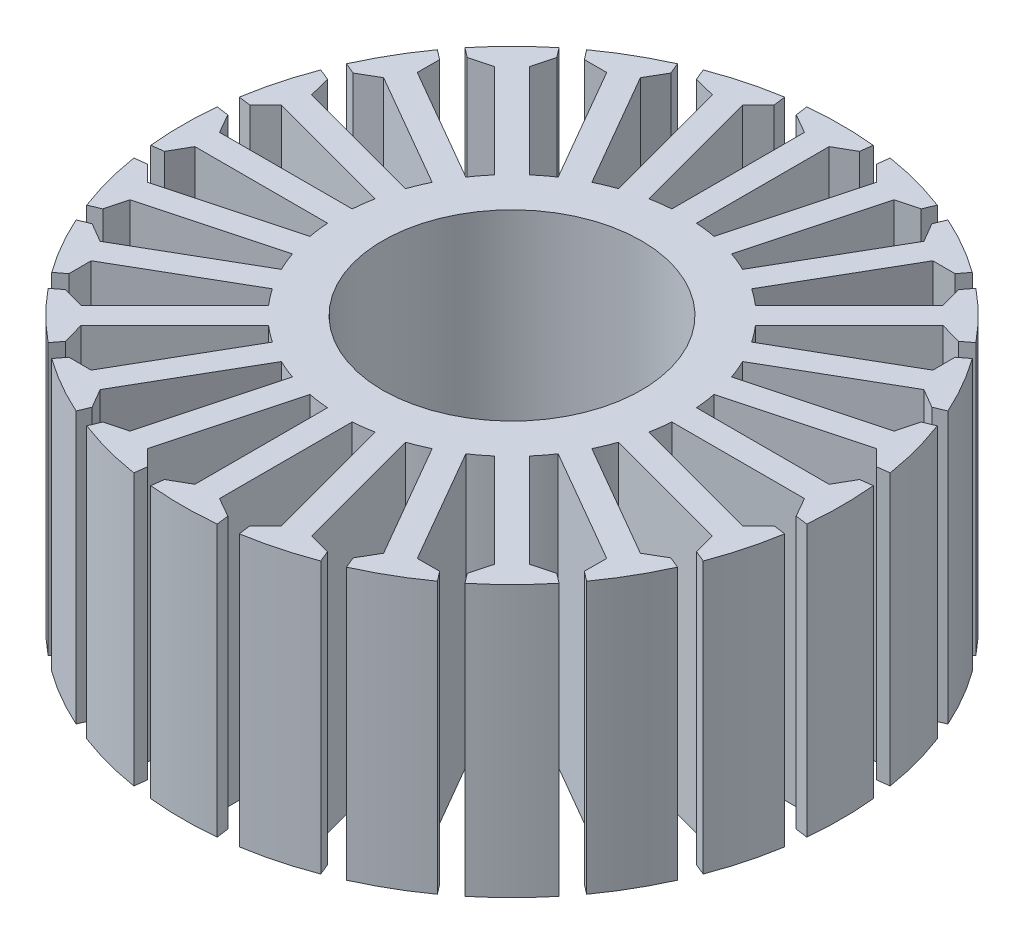
SolidWorks part; units mm, degrees
material "Ductile Iron"
ref_plane "Front Plane" through (0, 0, 0) normal (0, 0, 1) x (1, 0, 0)
ref_plane "Top Plane" through (0, 0, 0) normal (0, 1, 0) x (1, 0, 0)
ref_plane "Right Plane" through (0, 0, 0) normal (1, 0, 0) x (0, 0, -1)
sketch "Sketch3" plane through (0, 0, 0) normal (0, 1, 0) x (1, 0, 0)
  line L0 (0, 0) -> (0, 30) construction
  line L1 (0, 0) -> (8.452, 28.7848) construction
  line L2 (0, 0) -> (16.2192, 25.2376) construction
  line L3 (0, 0) -> (22.6725, 19.6458) construction
  line L4 (0, 0) -> (27.289, 12.4625) construction
  line L5 (0, 0) -> (29.6946, 4.2694) construction
  line L6 (0, 0) -> (29.6946, -4.2694) construction
  line L7 (0, 0) -> (27.289, -12.4625) construction
  line L8 (0, 0) -> (22.6725, -19.6458) construction
  line L9 (0, 0) -> (16.2192, -25.2376) construction
  line L10 (0, 0) -> (8.452, -28.7848) construction
  line L11 (0, 0) -> (0, -30) construction
  line L12 (0, 0) -> (-8.452, -28.7848) construction
  line L13 (0, 0) -> (-16.2192, -25.2376) construction
  line L14 (0, 0) -> (-22.6725, -19.6458) construction
  line L15 (0, 0) -> (-27.289, -12.4625) construction
  line L16 (0, 0) -> (-29.6946, -4.2694) construction
  line L17 (0, 0) -> (-29.6946, 4.2694) construction
  line L18 (0, 0) -> (-27.289, 12.4625) construction
  line L19 (0, 0) -> (-22.6725, 19.6458) construction
  line L20 (0, 0) -> (-16.2192, 25.2376) construction
  line L21 (0, 0) -> (-8.452, 28.7848) construction
  point P26 (0, 0)
  dimension "D1" = 30
  dimension "D2" = 22
sketch "Sketch1" plane through (0, 0, 0) normal (0, 1, 0) x (1, 0, 0)
  line L0 (0, 0) -> (0, 30) construction
  line L1 (3.5544, 26.788) -> (10.3158, 24.9762)
  line L2 (-3.5, 26.7951) -> (3.5, 26.7951)
  line L3 (-3.5, 26.7951) -> (-3.5, 29.7951)
  line L4 (-3.5, 29.7951) -> (3.5, 29.7951)
  line L5 (3.5, 26.7951) -> (3.5, 29.7951)
  line L6 (-3.5, 26.7951) -> (3.5, 29.7951) construction
  line L7 (-3.5, 29.7951) -> (3.5, 26.7951) construction
  line L8 (3.5544, 26.788) -> (4.3308, 29.6858)
  line L9 (4.3308, 29.6858) -> (11.0923, 27.874)
  line L10 (10.3158, 24.9762) -> (11.0923, 27.874)
  line L11 (3.5544, 26.788) -> (11.0923, 27.874) construction
  line L12 (4.3308, 29.6858) -> (10.3158, 24.9762) construction
  line L13 (10.3665, 24.9553) -> (16.4287, 21.4553)
  line L14 (10.3665, 24.9553) -> (11.8665, 27.5533)
  line L15 (11.8665, 27.5533) -> (17.9287, 24.0533)
  line L16 (16.4287, 21.4553) -> (17.9287, 24.0533)
  line L17 (10.3665, 24.9553) -> (17.9287, 24.0533) construction
  line L18 (11.8665, 27.5533) -> (16.4287, 21.4553) construction
  line L19 (16.4721, 21.4219) -> (21.4219, 16.4721)
  line L20 (16.4721, 21.4219) -> (18.5935, 23.5432)
  line L21 (18.5935, 23.5432) -> (23.5432, 18.5935)
  line L22 (21.4219, 16.4721) -> (23.5432, 18.5935)
  line L23 (16.4721, 21.4219) -> (23.5432, 18.5935) construction
  line L24 (18.5935, 23.5432) -> (21.4219, 16.4721) construction
  line L25 (21.4553, 16.4287) -> (24.9553, 10.3665)
  line L26 (21.4553, 16.4287) -> (24.0533, 17.9287)
  line L27 (24.0533, 17.9287) -> (27.5533, 11.8665)
  line L28 (24.9553, 10.3665) -> (27.5533, 11.8665)
  line L29 (21.4553, 16.4287) -> (27.5533, 11.8665) construction
  line L30 (24.0533, 17.9287) -> (24.9553, 10.3665) construction
  line L31 (24.9762, 10.3158) -> (26.788, 3.5544)
  line L32 (24.9762, 10.3158) -> (27.874, 11.0923)
  line L33 (27.874, 11.0923) -> (29.6858, 4.3308)
  line L34 (26.788, 3.5544) -> (29.6858, 4.3308)
  line L35 (24.9762, 10.3158) -> (29.6858, 4.3308) construction
  line L36 (27.874, 11.0923) -> (26.788, 3.5544) construction
  line L37 (26.7951, 3.5) -> (26.7951, -3.5)
  line L38 (26.7951, 3.5) -> (29.7951, 3.5)
  line L39 (29.7951, 3.5) -> (29.7951, -3.5)
  line L40 (26.7951, -3.5) -> (29.7951, -3.5)
  line L41 (26.7951, 3.5) -> (29.7951, -3.5) construction
  line L42 (29.7951, 3.5) -> (26.7951, -3.5) construction
  line L43 (26.788, -3.5544) -> (24.9762, -10.3158)
  line L44 (26.788, -3.5544) -> (29.6858, -4.3308)
  line L45 (29.6858, -4.3308) -> (27.874, -11.0923)
  line L46 (24.9762, -10.3158) -> (27.874, -11.0923)
  line L47 (26.788, -3.5544) -> (27.874, -11.0923) construction
  line L48 (29.6858, -4.3308) -> (24.9762, -10.3158) construction
  line L49 (24.9553, -10.3665) -> (21.4553, -16.4287)
  line L50 (24.9553, -10.3665) -> (27.5533, -11.8665)
  line L51 (27.5533, -11.8665) -> (24.0533, -17.9287)
  line L52 (21.4553, -16.4287) -> (24.0533, -17.9287)
  line L53 (24.9553, -10.3665) -> (24.0533, -17.9287) construction
  line L54 (27.5533, -11.8665) -> (21.4553, -16.4287) construction
  line L55 (21.4219, -16.4721) -> (16.4721, -21.4219)
  line L56 (21.4219, -16.4721) -> (23.5432, -18.5935)
  line L57 (23.5432, -18.5935) -> (18.5935, -23.5432)
  line L58 (16.4721, -21.4219) -> (18.5935, -23.5432)
  line L59 (21.4219, -16.4721) -> (18.5935, -23.5432) construction
  line L60 (23.5432, -18.5935) -> (16.4721, -21.4219) construction
  line L61 (16.4287, -21.4553) -> (10.3665, -24.9553)
  line L62 (16.4287, -21.4553) -> (17.9287, -24.0533)
  line L63 (17.9287, -24.0533) -> (11.8665, -27.5533)
  line L64 (10.3665, -24.9553) -> (11.8665, -27.5533)
  line L65 (16.4287, -21.4553) -> (11.8665, -27.5533) construction
  line L66 (17.9287, -24.0533) -> (10.3665, -24.9553) construction
  line L67 (10.3158, -24.9762) -> (3.5544, -26.788)
  line L68 (10.3158, -24.9762) -> (11.0923, -27.874)
  line L69 (11.0923, -27.874) -> (4.3308, -29.6858)
  line L70 (3.5544, -26.788) -> (4.3308, -29.6858)
  line L71 (10.3158, -24.9762) -> (4.3308, -29.6858) construction
  line L72 (11.0923, -27.874) -> (3.5544, -26.788) construction
  line L73 (3.5, -26.7951) -> (-3.5, -26.7951)
  line L74 (3.5, -26.7951) -> (3.5, -29.7951)
  line L75 (3.5, -29.7951) -> (-3.5, -29.7951)
  line L76 (-3.5, -26.7951) -> (-3.5, -29.7951)
  line L77 (3.5, -26.7951) -> (-3.5, -29.7951) construction
  line L78 (3.5, -29.7951) -> (-3.5, -26.7951) construction
  line L79 (-3.5544, -26.788) -> (-10.3158, -24.9762)
  line L80 (-3.5544, -26.788) -> (-4.3308, -29.6858)
  line L81 (-4.3308, -29.6858) -> (-11.0923, -27.874)
  line L82 (-10.3158, -24.9762) -> (-11.0923, -27.874)
  line L83 (-3.5544, -26.788) -> (-11.0923, -27.874) construction
  line L84 (-4.3308, -29.6858) -> (-10.3158, -24.9762) construction
  line L85 (-10.3665, -24.9553) -> (-16.4287, -21.4553)
  line L86 (-10.3665, -24.9553) -> (-11.8665, -27.5533)
  line L87 (-11.8665, -27.5533) -> (-17.9287, -24.0533)
  line L88 (-16.4287, -21.4553) -> (-17.9287, -24.0533)
  line L89 (-10.3665, -24.9553) -> (-17.9287, -24.0533) construction
  line L90 (-11.8665, -27.5533) -> (-16.4287, -21.4553) construction
  line L91 (-16.4721, -21.4219) -> (-21.4219, -16.4721)
  line L92 (-16.4721, -21.4219) -> (-18.5935, -23.5432)
  line L93 (-18.5935, -23.5432) -> (-23.5432, -18.5935)
  line L94 (-21.4219, -16.4721) -> (-23.5432, -18.5935)
  line L95 (-16.4721, -21.4219) -> (-23.5432, -18.5935) construction
  line L96 (-18.5935, -23.5432) -> (-21.4219, -16.4721) construction
  line L97 (-21.4553, -16.4287) -> (-24.9553, -10.3665)
  line L98 (-21.4553, -16.4287) -> (-24.0533, -17.9287)
  line L99 (-24.0533, -17.9287) -> (-27.5533, -11.8665)
  line L100 (-24.9553, -10.3665) -> (-27.5533, -11.8665)
  line L101 (-21.4553, -16.4287) -> (-27.5533, -11.8665) construction
  line L102 (-24.0533, -17.9287) -> (-24.9553, -10.3665) construction
  line L103 (-24.9762, -10.3158) -> (-26.788, -3.5544)
  line L104 (-24.9762, -10.3158) -> (-27.874, -11.0923)
  line L105 (-27.874, -11.0923) -> (-29.6858, -4.3308)
  line L106 (-26.788, -3.5544) -> (-29.6858, -4.3308)
  line L107 (-24.9762, -10.3158) -> (-29.6858, -4.3308) construction
  line L108 (-27.874, -11.0923) -> (-26.788, -3.5544) construction
  line L109 (-26.7951, -3.5) -> (-26.7951, 3.5)
  line L110 (-26.7951, -3.5) -> (-29.7951, -3.5)
  line L111 (-29.7951, -3.5) -> (-29.7951, 3.5)
  line L112 (-26.7951, 3.5) -> (-29.7951, 3.5)
  line L113 (-26.7951, -3.5) -> (-29.7951, 3.5) construction
  line L114 (-29.7951, -3.5) -> (-26.7951, 3.5) construction
  line L115 (-26.788, 3.5544) -> (-24.9762, 10.3158)
  line L116 (-26.788, 3.5544) -> (-29.6858, 4.3308)
  line L117 (-29.6858, 4.3308) -> (-27.874, 11.0923)
  line L118 (-24.9762, 10.3158) -> (-27.874, 11.0923)
  line L119 (-26.788, 3.5544) -> (-27.874, 11.0923) construction
  line L120 (-29.6858, 4.3308) -> (-24.9762, 10.3158) construction
  line L121 (-24.9553, 10.3665) -> (-21.4553, 16.4287)
  line L122 (-24.9553, 10.3665) -> (-27.5533, 11.8665)
  line L123 (-27.5533, 11.8665) -> (-24.0533, 17.9287)
  line L124 (-21.4553, 16.4287) -> (-24.0533, 17.9287)
  line L125 (-24.9553, 10.3665) -> (-24.0533, 17.9287) construction
  line L126 (-27.5533, 11.8665) -> (-21.4553, 16.4287) construction
  line L127 (-21.4219, 16.4721) -> (-16.4721, 21.4219)
  line L128 (-21.4219, 16.4721) -> (-23.5432, 18.5935)
  line L129 (-23.5432, 18.5935) -> (-18.5935, 23.5432)
  line L130 (-16.4721, 21.4219) -> (-18.5935, 23.5432)
  line L131 (-21.4219, 16.4721) -> (-18.5935, 23.5432) construction
  line L132 (-23.5432, 18.5935) -> (-16.4721, 21.4219) construction
  line L133 (-16.4287, 21.4553) -> (-10.3665, 24.9553)
  line L134 (-16.4287, 21.4553) -> (-17.9287, 24.0533)
  line L135 (-17.9287, 24.0533) -> (-11.8665, 27.5533)
  line L136 (-10.3665, 24.9553) -> (-11.8665, 27.5533)
  line L137 (-16.4287, 21.4553) -> (-11.8665, 27.5533) construction
  line L138 (-17.9287, 24.0533) -> (-10.3665, 24.9553) construction
  line L139 (-10.3158, 24.9762) -> (-3.5544, 26.788)
  line L140 (-10.3158, 24.9762) -> (-11.0923, 27.874)
  line L141 (-11.0923, 27.874) -> (-4.3308, 29.6858)
  line L142 (-3.5544, 26.788) -> (-4.3308, 29.6858)
  line L143 (-10.3158, 24.9762) -> (-4.3308, 29.6858) construction
  line L144 (-11.0923, 27.874) -> (-3.5544, 26.788) construction
  circle A0 centre (0, 0) radius 32.5
  circle A1 centre (0, 0) radius 30
  circle A2 centre (0, 0) radius 10
  circle A3 centre (0, 0) radius 26.6
  point P5 (0, 28.2951)
  point P10 (7.3233, 27.331)
  point P17 (14.1476, 24.5043)
  point P22 (20.0077, 20.0077)
  point P27 (24.5043, 14.1476)
  point P32 (27.331, 7.3233)
  point P37 (28.2951, 0)
  point P42 (27.331, -7.3233)
  point P47 (24.5043, -14.1476)
  point P52 (20.0077, -20.0077)
  point P57 (14.1476, -24.5043)
  point P62 (7.3233, -27.331)
  point P67 (0, -28.2951)
  point P72 (-7.3233, -27.331)
  point P77 (-14.1476, -24.5043)
  point P82 (-20.0077, -20.0077)
  point P87 (-24.5043, -14.1476)
  point P92 (-27.331, -7.3233)
  point P97 (-28.2951, 0)
  point P102 (-27.331, 7.3233)
  point P107 (-24.5043, 14.1476)
  point P112 (-20.0077, 20.0077)
  point P117 (-14.1476, 24.5043)
  point P122 (-7.3233, 27.331)
  point P127 (0, 0)
  dimension "D1" = 65
  dimension "D2" = 60
  dimension "D5" = 20
  dimension "D8" = 53.2
  dimension "D3" = 3
  dimension "D4" = 7
sketch "Sketch4" plane through (0, 0, 0) normal (0, 1, 0) x (1, 0, 0)
  line L0 (0, 0) -> (0, 30) construction
  line L1 (0, 0) -> (0, 24.6)
  line L2 (0, 0) -> (-8.452, 28.7848) construction
  line L3 (0, 0) -> (-6.9306, 23.6035)
  line L5 (-3.7856, 26.3293) -> (0, 0) construction
  line L6 (-4.5264, 26.212) -> (-4.2417, 24.2316)
  line L7 (-3.0417, 26.4255) -> (-2.757, 24.445)
  line L8 (-3.4836, 29.4991) -> (0.7424, 0.1067) construction
  line L9 (-4.226, 29.3924) -> (0, 0) construction
  line L10 (-4.9684, 29.2857) -> (-0.7424, -0.1067) construction
  line L11 (1, -6.9552) -> (-7.8901, 23.3218)
  line L12 (1, -6.9552) -> (1, 24.6)
  line L13 (-1, 6.9552) -> (-5.9711, 23.8853)
  line L14 (-1, 6.9552) -> (-1, 24.6)
  circle A0 centre (0, 0) radius 26.6 construction
  circle A1 centre (0, 0) radius 26.6
  circle A2 centre (0, 0) radius 24.6
  circle A3 centre (0, 0) radius 14
  dimension "D3" = 1
  dimension "D5" = 28
  dimension "D1" = 0.75
  dimension "D2" = 0.75
  dimension "D4" = 1
sketch "Sketch5" plane through (0, 0, 0) normal (0, 1, 0) x (1, 0, 0)
  line L0 (0, 0) -> (0, 12.5) construction
  line L160 (-1, 13.9642) -> (-1, 24.7298)
  line L161 (1, 24.7298) -> (2.5687, 25.6269)
  line L162 (-2.5687, 25.6269) -> (-2.7, 26.624)
  line L163 (-1, 24.7298) -> (-2.5687, 25.6269)
  line L164 (2.5687, 25.6269) -> (2.7, 26.624)
  line L165 (2.6483, 13.7472) -> (5.4346, 24.146)
  line L166 (7.3665, 23.6283) -> (9.1139, 24.0888)
  line L167 (1, 13.9642) -> (1, 24.7298)
  line L168 (4.1515, 25.4185) -> (4.2828, 26.4156)
  line L169 (5.4346, 24.146) -> (4.1515, 25.4185)
  line L170 (9.1139, 24.0888) -> (9.4988, 25.018)
  line L171 (4.5801, 13.2296) -> (7.3665, 23.6283)
  line L172 (6.1161, 12.5934) -> (11.4989, 21.9166)
  line L173 (13.2309, 20.9166) -> (15.038, 20.9092)
  line L174 (10.5889, 23.4779) -> (10.9737, 24.407)
  line L175 (11.4989, 21.9166) -> (10.5889, 23.4779)
  line L176 (15.038, 20.9092) -> (15.6502, 21.707)
  line L177 (7.8481, 11.5934) -> (13.2309, 20.9166)
  line L178 (9.1671, 10.5813) -> (16.7795, 18.1937)
  line L179 (18.1937, 16.7795) -> (19.9373, 16.3046)
  line L180 (16.3046, 19.9373) -> (16.9168, 20.7351)
  line L181 (16.7795, 18.1937) -> (16.3046, 19.9373)
  line L182 (19.9373, 16.3046) -> (20.7351, 16.9168)
  line L183 (10.5813, 9.1671) -> (18.1937, 16.7795)
  line L184 (11.5934, 7.8481) -> (20.9166, 13.2309)
  line L185 (21.9166, 11.4989) -> (23.4779, 10.5889)
  line L186 (20.9092, 15.038) -> (21.707, 15.6502)
  line L187 (20.9166, 13.2309) -> (20.9092, 15.038)
  line L188 (23.4779, 10.5889) -> (24.407, 10.9737)
  line L189 (12.5934, 6.1161) -> (21.9166, 11.4989)
  line L190 (13.2296, 4.5801) -> (23.6283, 7.3665)
  line L191 (24.146, 5.4346) -> (25.4185, 4.1515)
  line L192 (24.0888, 9.1139) -> (25.018, 9.4988)
  line L193 (23.6283, 7.3665) -> (24.0888, 9.1139)
  line L194 (25.4185, 4.1515) -> (26.4156, 4.2828)
  line L195 (13.7472, 2.6483) -> (24.146, 5.4346)
  line L196 (13.9642, 1) -> (24.7298, 1)
  line L197 (24.7298, -1) -> (25.6269, -2.5687)
  line L198 (25.6269, 2.5687) -> (26.624, 2.7)
  line L199 (24.7298, 1) -> (25.6269, 2.5687)
  line L200 (25.6269, -2.5687) -> (26.624, -2.7)
  line L201 (13.9642, -1) -> (24.7298, -1)
  line L202 (13.7472, -2.6483) -> (24.146, -5.4346)
  line L203 (23.6283, -7.3665) -> (24.0888, -9.1139)
  line L204 (25.4185, -4.1515) -> (26.4156, -4.2828)
  line L205 (24.146, -5.4346) -> (25.4185, -4.1515)
  line L206 (24.0888, -9.1139) -> (25.018, -9.4988)
  line L207 (13.2296, -4.5801) -> (23.6283, -7.3665)
  line L208 (12.5934, -6.1161) -> (21.9166, -11.4989)
  line L209 (20.9166, -13.2309) -> (20.9092, -15.038)
  line L210 (23.4779, -10.5889) -> (24.407, -10.9737)
  line L211 (21.9166, -11.4989) -> (23.4779, -10.5889)
  line L212 (20.9092, -15.038) -> (21.707, -15.6502)
  line L213 (11.5934, -7.8481) -> (20.9166, -13.2309)
  line L214 (10.5813, -9.1671) -> (18.1937, -16.7795)
  line L215 (16.7795, -18.1937) -> (16.3046, -19.9373)
  line L216 (19.9373, -16.3046) -> (20.7351, -16.9168)
  line L217 (18.1937, -16.7795) -> (19.9373, -16.3046)
  line L218 (16.3046, -19.9373) -> (16.9168, -20.7351)
  line L219 (9.1671, -10.5813) -> (16.7795, -18.1937)
  line L220 (7.8481, -11.5934) -> (13.2309, -20.9166)
  line L221 (11.4989, -21.9166) -> (10.5889, -23.4779)
  line L222 (15.038, -20.9092) -> (15.6502, -21.707)
  line L223 (13.2309, -20.9166) -> (15.038, -20.9092)
  line L224 (10.5889, -23.4779) -> (10.9737, -24.407)
  line L225 (6.1161, -12.5934) -> (11.4989, -21.9166)
  line L226 (4.5801, -13.2296) -> (7.3665, -23.6283)
  line L227 (5.4346, -24.146) -> (4.1515, -25.4185)
  line L228 (9.1139, -24.0888) -> (9.4988, -25.018)
  line L229 (7.3665, -23.6283) -> (9.1139, -24.0888)
  line L230 (4.1515, -25.4185) -> (4.2828, -26.4156)
  line L231 (2.6483, -13.7472) -> (5.4346, -24.146)
  line L232 (1, -13.9642) -> (1, -24.7298)
  line L233 (-1, -24.7298) -> (-2.5687, -25.6269)
  line L234 (2.5687, -25.6269) -> (2.7, -26.624)
  line L235 (1, -24.7298) -> (2.5687, -25.6269)
  line L236 (-2.5687, -25.6269) -> (-2.7, -26.624)
  line L237 (-1, -13.9642) -> (-1, -24.7298)
  line L238 (-2.6483, -13.7472) -> (-5.4346, -24.146)
  line L239 (-7.3665, -23.6283) -> (-9.1139, -24.0888)
  line L240 (-4.1515, -25.4185) -> (-4.2828, -26.4156)
  line L241 (-5.4346, -24.146) -> (-4.1515, -25.4185)
  line L242 (-9.1139, -24.0888) -> (-9.4988, -25.018)
  line L243 (-4.5801, -13.2296) -> (-7.3665, -23.6283)
  line L244 (-6.1161, -12.5934) -> (-11.4989, -21.9166)
  line L245 (-13.2309, -20.9166) -> (-15.038, -20.9092)
  line L246 (-10.5889, -23.4779) -> (-10.9737, -24.407)
  line L247 (-11.4989, -21.9166) -> (-10.5889, -23.4779)
  line L248 (-15.038, -20.9092) -> (-15.6502, -21.707)
  line L249 (-7.8481, -11.5934) -> (-13.2309, -20.9166)
  line L250 (-9.1671, -10.5813) -> (-16.7795, -18.1937)
  line L251 (-18.1937, -16.7795) -> (-19.9373, -16.3046)
  line L252 (-16.3046, -19.9373) -> (-16.9168, -20.7351)
  line L253 (-16.7795, -18.1937) -> (-16.3046, -19.9373)
  line L254 (-19.9373, -16.3046) -> (-20.7351, -16.9168)
  line L255 (-10.5813, -9.1671) -> (-18.1937, -16.7795)
  line L256 (-11.5934, -7.8481) -> (-20.9166, -13.2309)
  line L257 (-21.9166, -11.4989) -> (-23.4779, -10.5889)
  line L258 (-20.9092, -15.038) -> (-21.707, -15.6502)
  line L259 (-20.9166, -13.2309) -> (-20.9092, -15.038)
  line L260 (-23.4779, -10.5889) -> (-24.407, -10.9737)
  line L261 (-12.5934, -6.1161) -> (-21.9166, -11.4989)
  line L262 (-13.2296, -4.5801) -> (-23.6283, -7.3665)
  line L263 (-24.146, -5.4346) -> (-25.4185, -4.1515)
  line L264 (-24.0888, -9.1139) -> (-25.018, -9.4988)
  line L265 (-23.6283, -7.3665) -> (-24.0888, -9.1139)
  line L266 (-25.4185, -4.1515) -> (-26.4156, -4.2828)
  line L267 (-13.7472, -2.6483) -> (-24.146, -5.4346)
  line L268 (-13.9642, -1) -> (-24.7298, -1)
  line L269 (-24.7298, 1) -> (-25.6269, 2.5687)
  line L270 (-25.6269, -2.5687) -> (-26.624, -2.7)
  line L271 (-24.7298, -1) -> (-25.6269, -2.5687)
  line L272 (-25.6269, 2.5687) -> (-26.624, 2.7)
  line L273 (-13.9642, 1) -> (-24.7298, 1)
  line L274 (-13.7472, 2.6483) -> (-24.146, 5.4346)
  line L275 (-23.6283, 7.3665) -> (-24.0888, 9.1139)
  line L276 (-25.4185, 4.1515) -> (-26.4156, 4.2828)
  line L277 (-24.146, 5.4346) -> (-25.4185, 4.1515)
  line L278 (-24.0888, 9.1139) -> (-25.018, 9.4988)
  line L279 (-13.2296, 4.5801) -> (-23.6283, 7.3665)
  line L280 (-12.5934, 6.1161) -> (-21.9166, 11.4989)
  line L281 (-20.9166, 13.2309) -> (-20.9092, 15.038)
  line L282 (-23.4779, 10.5889) -> (-24.407, 10.9737)
  line L283 (-21.9166, 11.4989) -> (-23.4779, 10.5889)
  line L284 (-20.9092, 15.038) -> (-21.707, 15.6502)
  line L285 (-11.5934, 7.8481) -> (-20.9166, 13.2309)
  line L286 (-10.5813, 9.1671) -> (-18.1937, 16.7795)
  line L287 (-16.7795, 18.1937) -> (-16.3046, 19.9373)
  line L288 (-19.9373, 16.3046) -> (-20.7351, 16.9168)
  line L289 (-18.1937, 16.7795) -> (-19.9373, 16.3046)
  line L290 (-16.3046, 19.9373) -> (-16.9168, 20.7351)
  line L291 (-9.1671, 10.5813) -> (-16.7795, 18.1937)
  line L292 (-7.8481, 11.5934) -> (-13.2309, 20.9166)
  line L293 (-11.4989, 21.9166) -> (-10.5889, 23.4779)
  line L294 (-15.038, 20.9092) -> (-15.6502, 21.707)
  line L295 (-13.2309, 20.9166) -> (-15.038, 20.9092)
  line L296 (-10.5889, 23.4779) -> (-10.9737, 24.407)
  line L297 (-6.1161, 12.5934) -> (-11.4989, 21.9166)
  line L298 (-4.5801, 13.2296) -> (-7.3665, 23.6283)
  line L299 (-5.4346, 24.146) -> (-4.1515, 25.4185)
  line L300 (-9.1139, 24.0888) -> (-9.4988, 25.018)
  line L301 (-7.3665, 23.6283) -> (-9.1139, 24.0888)
  line L302 (-4.1515, 25.4185) -> (-4.2828, 26.4156)
  line L303 (-2.6483, 13.7472) -> (-5.4346, 24.146)
  line L304 (0, 14) -> (0, 26.75) construction
  circle A0 centre (0, 0) radius 14 construction
  circle A3 centre (0, 0) radius 14 construction
  circle A48 centre (0, 0) radius 10.5
  arc A49 (2.6986, 26.6135) -> (-2.6986, 26.6135) centre (0, 0) ccw
  arc A50 (9.4947, 25.0082) -> (4.2814, 26.4051) centre (0, 0) ccw
  arc A51 (15.6438, 21.6987) -> (10.9697, 24.3973) centre (0, 0) ccw
  arc A52 (20.7268, 16.9104) -> (16.9104, 20.7268) centre (0, 0) ccw
  arc A53 (24.3973, 10.9697) -> (21.6987, 15.6438) centre (0, 0) ccw
  arc A54 (26.4051, 4.2814) -> (25.0082, 9.4947) centre (0, 0) ccw
  arc A55 (26.6135, -2.6986) -> (26.6135, 2.6986) centre (0, 0) ccw
  arc A56 (25.0082, -9.4947) -> (26.4051, -4.2814) centre (0, 0) ccw
  arc A57 (21.6987, -15.6438) -> (24.3973, -10.9697) centre (0, 0) ccw
  arc A58 (16.9104, -20.7268) -> (20.7268, -16.9104) centre (0, 0) ccw
  arc A59 (10.9697, -24.3973) -> (15.6438, -21.6987) centre (0, 0) ccw
  arc A60 (4.2814, -26.4051) -> (9.4947, -25.0082) centre (0, 0) ccw
  arc A61 (-2.6986, -26.6135) -> (2.6986, -26.6135) centre (0, 0) ccw
  arc A62 (-9.4947, -25.0082) -> (-4.2814, -26.4051) centre (0, 0) ccw
  arc A63 (-15.6438, -21.6987) -> (-10.9697, -24.3973) centre (0, 0) ccw
  arc A64 (-20.7268, -16.9104) -> (-16.9104, -20.7268) centre (0, 0) ccw
  arc A65 (-24.3973, -10.9697) -> (-21.6987, -15.6438) centre (0, 0) ccw
  arc A66 (-26.4051, -4.2814) -> (-25.0082, -9.4947) centre (0, 0) ccw
  arc A67 (-26.6135, 2.6986) -> (-26.6135, -2.6986) centre (0, 0) ccw
  arc A68 (-25.0082, 9.4947) -> (-26.4051, 4.2814) centre (0, 0) ccw
  arc A69 (-21.6987, 15.6438) -> (-24.3973, 10.9697) centre (0, 0) ccw
  arc A70 (-16.9104, 20.7268) -> (-20.7268, 16.9104) centre (0, 0) ccw
  arc A71 (-10.9697, 24.3973) -> (-15.6438, 21.6987) centre (0, 0) ccw
  arc A72 (-4.2814, 26.4051) -> (-9.4947, 25.0082) centre (0, 0) ccw
  arc A73 (6.1161, 12.5934) -> (4.5801, 13.2296) centre (0, 0) ccw
  arc A74 (2.6483, 13.7472) -> (1, 13.9642) centre (0, 0) ccw
  arc A75 (-1, 13.9642) -> (-2.6483, 13.7472) centre (0, 0) ccw
  arc A76 (-4.5801, 13.2296) -> (-6.1161, 12.5934) centre (0, 0) ccw
  arc A77 (-7.8481, 11.5934) -> (-9.1671, 10.5813) centre (0, 0) ccw
  arc A78 (-10.5813, 9.1671) -> (-11.5934, 7.8481) centre (0, 0) ccw
  arc A79 (-12.5934, 6.1161) -> (-13.2296, 4.5801) centre (0, 0) ccw
  arc A80 (-13.7472, 2.6483) -> (-13.9642, 1) centre (0, 0) ccw
  arc A81 (-13.9642, -1) -> (-13.7472, -2.6483) centre (0, 0) ccw
  arc A82 (-13.2296, -4.5801) -> (-12.5934, -6.1161) centre (0, 0) ccw
  arc A83 (-11.5934, -7.8481) -> (-10.5813, -9.1671) centre (0, 0) ccw
  arc A84 (-9.1671, -10.5813) -> (-7.8481, -11.5934) centre (0, 0) ccw
  arc A85 (-6.1161, -12.5934) -> (-4.5801, -13.2296) centre (0, 0) ccw
  arc A86 (-2.6483, -13.7472) -> (-1, -13.9642) centre (0, 0) ccw
  arc A87 (1, -13.9642) -> (2.6483, -13.7472) centre (0, 0) ccw
  arc A88 (4.5801, -13.2296) -> (6.1161, -12.5934) centre (0, 0) ccw
  arc A89 (7.8481, -11.5934) -> (9.1671, -10.5813) centre (0, 0) ccw
  arc A90 (10.5813, -9.1671) -> (11.5934, -7.8481) centre (0, 0) ccw
  arc A91 (12.5934, -6.1161) -> (13.2296, -4.5801) centre (0, 0) ccw
  arc A92 (13.7472, -2.6483) -> (13.9642, -1) centre (0, 0) ccw
  arc A93 (13.9642, 1) -> (13.7472, 2.6483) centre (0, 0) ccw
  arc A94 (13.2296, 4.5801) -> (12.5934, 6.1161) centre (0, 0) ccw
  arc A95 (11.5934, 7.8481) -> (10.5813, 9.1671) centre (0, 0) ccw
  arc A96 (9.1671, 10.5813) -> (7.8481, 11.5934) centre (0, 0) ccw
  point P473 (0, 0)
  dimension "D6" = 28
  dimension "D4" = 2
  dimension "D5" = 7.5
extrude "Boss-Extrude1" add sketch "Sketch5" along normal blind 22 contours L178 A96 L177 L173 L176 A51 L174 L175 L172 A73 L171 L166 L170 A50 L168 L169 L165 A74 L167 L161 L164 A49 L162 L163 L160 A75 L303 L299 L302 A72 L300 L301 L298 A76 L297 L293 L296 A71 L294 L295 L292 A77 L291 L287 L290 A70 L288 L289 L286 A78 L285
